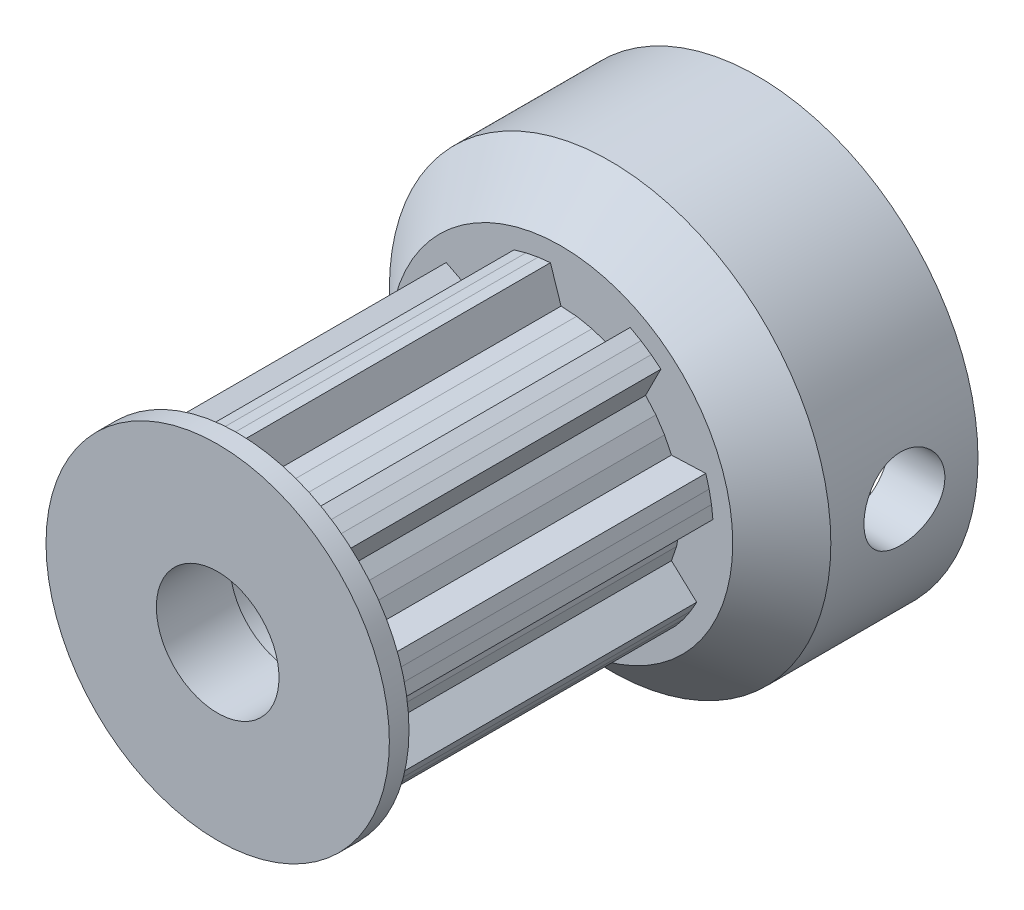
SolidWorks part; units mm, degrees
material "Green ABS"
ref_plane "Front Plane" through (0, 0, 0) normal (0, 0, 1) x (1, 0, 0)
ref_plane "Top Plane" through (0, 0, 0) normal (0, 1, 0) x (1, 0, 0)
ref_plane "Right Plane" through (0, 0, 0) normal (1, 0, 0) x (0, 0, -1)
sketch "Sketch2" plane through (0, 0, 0) normal (0, 0, 1) x (1, 0, 0)
  line L2 (4.8737, 0) -> (4.832, -0.6361)
  line L3 (4.832, -0.6361) -> (4.7076, -1.2614)
  line L7 (4.7076, -1.2614) -> (4.5027, -1.8651)
  line L18 (5.529, -2.8172) -> (5.2815, -3.2577)
  line L20 (4.5027, -1.8651) -> (5.529, -2.8172)
  line L25 (5.2815, -3.2577) -> (4.999, -3.6766)
  line L27 (4.6833, -4.0711) -> (3.4462, -3.4462)
  line L29 (4.999, -3.6766) -> (4.6833, -4.0711)
  line L30 (3.4462, -3.4462) -> (2.9669, -3.8666)
  line L34 (2.9669, -3.8666) -> (2.4369, -4.2208)
  line L37 (2.4369, -4.2208) -> (1.8651, -4.5027)
  line L43 (0, -4.8737) -> (-0.6361, -4.832)
  line L46 (-0.6361, -4.832) -> (-1.2614, -4.7076)
  line L49 (-1.2614, -4.7076) -> (-1.8651, -4.5027)
  line L56 (-3.4462, -3.4462) -> (-3.8666, -2.9669)
  line L57 (-3.8666, -2.9669) -> (-4.2208, -2.4369)
  line L61 (-4.2208, -2.4369) -> (-4.5027, -1.8651)
  line L68 (-4.8737, 0) -> (-4.832, 0.6361)
  line L69 (-4.832, 0.6361) -> (-4.7076, 1.2614)
  line L73 (-4.7076, 1.2614) -> (-4.5027, 1.8651)
  line L84 (1.9176, -5.9017) -> (1.4311, -6.0381)
  line L86 (1.8651, -4.5027) -> (1.9176, -5.9017)
  line L91 (1.4311, -6.0381) -> (0.9351, -6.1345)
  line L93 (0.4329, -6.1903) -> (0, -4.8737)
  line L95 (0.9351, -6.1345) -> (0.4329, -6.1903)
  line L96 (-2.8172, -5.529) -> (-3.2577, -5.2815)
  line L98 (-1.8651, -4.5027) -> (-2.8172, -5.529)
  line L100 (-3.2577, -5.2815) -> (-3.6766, -4.999)
  line L103 (-3.6766, -4.999) -> (-4.0711, -4.6833)
  line L104 (-4.0711, -4.6833) -> (-3.4462, -3.4462)
  line L108 (-5.9017, -1.9176) -> (-6.0381, -1.4311)
  line L110 (-4.5027, -1.8651) -> (-5.9017, -1.9176)
  line L115 (-6.0381, -1.4311) -> (-6.1345, -0.9351)
  line L117 (-6.1903, -0.4329) -> (-4.8737, 0)
  line L119 (-6.1345, -0.9351) -> (-6.1903, -0.4329)
  line L120 (-5.529, 2.8172) -> (-5.2815, 3.2577)
  line L122 (-4.5027, 1.8651) -> (-5.529, 2.8172)
  line L127 (-5.2815, 3.2577) -> (-4.999, 3.6766)
  line L129 (-4.6833, 4.0711) -> (-3.4462, 3.4462)
  line L131 (-4.999, 3.6766) -> (-4.6833, 4.0711)
  line L132 (-3.4462, 3.4462) -> (-2.9669, 3.8666)
  line L136 (-2.9669, 3.8666) -> (-2.4369, 4.2208)
  line L139 (-2.4369, 4.2208) -> (-1.8651, 4.5027)
  line L145 (0, 4.8737) -> (0.6361, 4.832)
  line L148 (0.6361, 4.832) -> (1.2614, 4.7076)
  line L151 (1.2614, 4.7076) -> (1.8651, 4.5027)
  line L158 (3.4462, 3.4462) -> (3.8666, 2.9669)
  line L159 (3.8666, 2.9669) -> (4.2208, 2.4369)
  line L163 (4.2208, 2.4369) -> (4.5027, 1.8651)
  line L171 (-1.9176, 5.9017) -> (-1.4311, 6.0381)
  line L173 (-1.8651, 4.5027) -> (-1.9176, 5.9017)
  line L178 (-1.4311, 6.0381) -> (-0.9351, 6.1345)
  line L180 (-0.4329, 6.1903) -> (0, 4.8737)
  line L182 (-0.9351, 6.1345) -> (-0.4329, 6.1903)
  line L183 (2.8172, 5.529) -> (3.2577, 5.2815)
  line L185 (1.8651, 4.5027) -> (2.8172, 5.529)
  line L187 (3.2577, 5.2815) -> (3.6766, 4.999)
  line L190 (3.6766, 4.999) -> (4.0711, 4.6833)
  line L191 (4.0711, 4.6833) -> (3.4462, 3.4462)
  line L195 (5.9017, 1.9176) -> (6.0381, 1.4311)
  line L197 (4.5027, 1.8651) -> (5.9017, 1.9176)
  line L199 (6.0381, 1.4311) -> (6.1345, 0.9351)
  line L202 (6.1345, 0.9351) -> (6.1903, 0.4329)
  line L203 (6.1903, 0.4329) -> (4.8737, 0)
  circle A0 centre (0, 0) radius 2.625
  dimension "D1" = 5.25
extrude "Boss-Extrude1" add sketch "Sketch2" along normal blind 14
sketch "Sketch3" plane through (0, 0, 0) normal (0, 0, -1) x (-1, 0, 0)
  circle A0 centre (0, 0) radius 9
  dimension "D1" = 18
extrude "Boss-Extrude2" add sketch "Sketch3" along normal blind 8
sketch "Sketch4" plane through (0, 0, -8) normal (0, 0, -1) x (-1, 0, 0)
  circle A0 centre (0, 0) radius 2.5
extrude "Cut-Extrude1" cut sketch "Sketch4" against normal through all
sketch "Sketch5" plane through (0, 0, 0) normal (0, 1, 0) x (1, 0, 0)
  line L0 (0, 0) -> (0, -15.7839) construction
  line L1 (2.5, -14) -> (7, -14)
  line L2 (7, -14) -> (7, -13.2)
  line L3 (7, -13.2) -> (2.5, -11)
  line L5 (2.5, -11) -> (2.5, -14)
  dimension "D1" = 7
  dimension "D2" = 0.8
  dimension "D3" = 3
  dimension "D4" = 2.5
revolve "Revolve1" add sketch "Sketch5" angle 360 about L0
chamfer "Chamfer1" distance 2 angle 45 1 edges at (-9, 0, 0)
ref_plane "Plane1" through (9, 0, 0) normal (1, 0, 0) x (0, 0, -1)
ref_plane "Plane2" through (4, 0, 0) normal (1, 0, 0) x (0, 0, -1)
sketch "Sketch6" plane through (4, 0, 0) normal (1, 0, 0) x (0, 0, -1)
  line L0 (0, 0) -> (10, 0) construction
  line L1 (8, 2.9) -> (8, -2.9)
  line L2 (1.6514, 0) -> (3.3257, -2.9)
  line L3 (3.3257, -2.9) -> (8, -2.9)
  line L6 (8, 2.9) -> (3.3257, 2.9)
  line L7 (3.3257, 2.9) -> (1.6514, 0)
  line L8 (8, -9) -> (8, 9) construction
  line L10 (7.8317, -0.8953) -> (8.9519, 1.0448) [skipped]
  line L11 (7.8317, 0.8953) -> (6.7116, 2.8354) [skipped]
  circle A0 centre (5, 0) radius 2.9 construction
  dimension "D1" = 5.8
  dimension "D2" = 3
extrude "Cut-Extrude2" cut sketch "Sketch6" along normal blind 2.7
sketch "Sketch7" plane through (9, 0, 0) normal (1, 0, 0) x (0, 0, -1)
  line L0 (3.3257, 2.9) -> (1.6514, 0) construction
  line L1 (1.6514, 0) -> (3.3257, -2.9) construction
  circle A0 centre (5, 0) radius 2.9 construction
  circle A1 centre (5, 0) radius 1.65
  dimension "D1" = 5.8
  dimension "D2" = 3.3
extrude "Cut-Extrude3" cut sketch "Sketch7" against normal up to surface (6.5 mm away)
chamfer "Chamfer2" distance 0.5 angle 45 2 edges at (5.35, -2.9, -8) (5.35, 2.9, -8)
chamfer "Chamfer3" distance 0.5 angle 45 1 edges at (-2.5, 0, -8)
